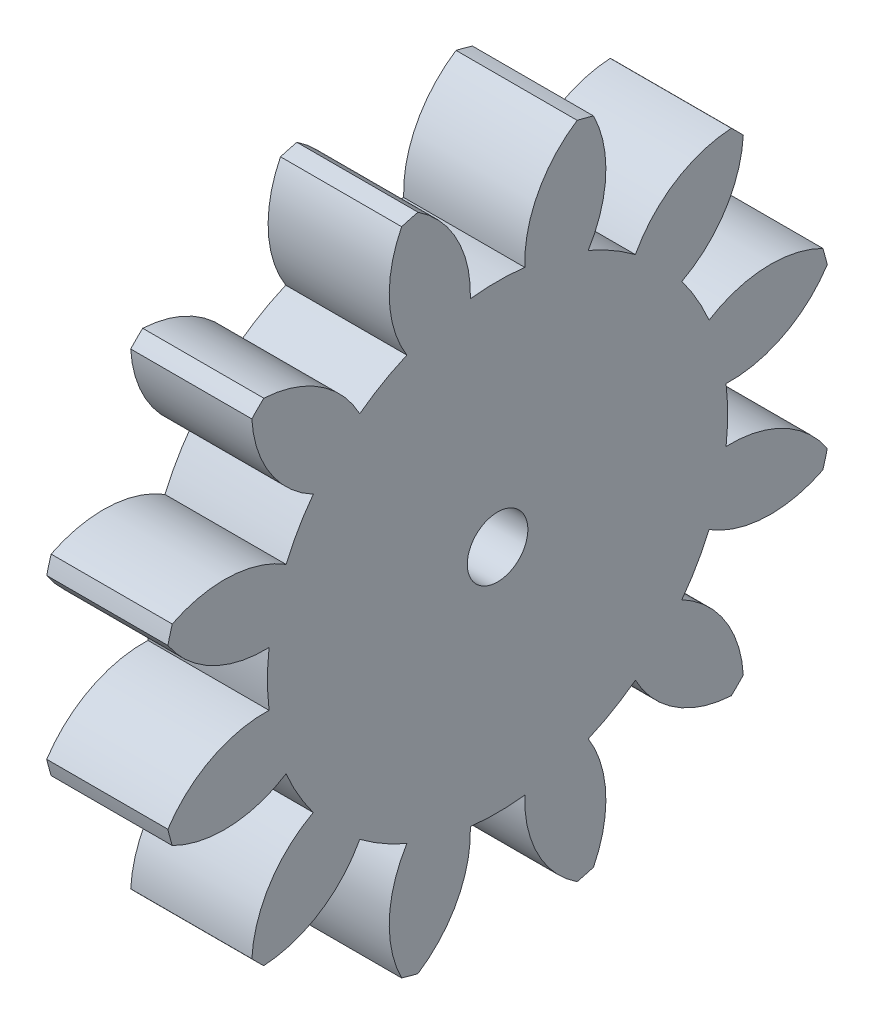
SolidWorks part; units mm, degrees
ref_plane "Plane1" through (0, 0, 0) normal (0, 0, 1) x (1, 0, 0)
ref_plane "Plane2" through (0, 0, 0) normal (0, 1, 0) x (1, 0, 0)
ref_plane "Plane3" through (0, 0, 0) normal (1, 0, 0) x (0, 0, -1)
other "Configuration Table"
sketch "HoldingSke" plane through (0, 0, 0) normal (0, 1, 0) x (1, 0, 0)
  line L0 (0, 0) -> (124.2247, -26.4048)
  line L1 (-15, 0) -> (100, 0) construction
  line L2 (0, 0) -> (-2.1039, 2.3779)
  line L3 (0, 0) -> (-11.863, 4.5341)
  line L4 (0, 0) -> (8.4473, 1.7955)
  line L5 (0, 0) -> (-47.5972, -17.7524)
  line L6 (0, 0) -> (-10.5278, -7.1032)
  line L7 (-2.1039, 2.3779) -> (8.8308, 51.9871)
  line L8 (-76.2, 54.61) -> (-69.596, 54.61)
  line L9 (-71.009, 38.7566) -> (-53.1078, 45.2721)
  line L10 (-76.2, 71.12) -> (104.1128, 71.12)
  line L11 (0, 0) -> (-12.7, 0)
  line L12 (-76.2, 101.6) -> (-76.0095, 101.6)
  line L13 (24.9733, 27.94) -> (52.9518, 28.4284)
  line L14 (24.9733, 27.94) -> (24.9746, 27.94)
  line L15 (24.9733, 27.94) -> (100.4006, 29.5858)
  circle A0 centre (0, 0) radius 3.175
  circle A1 centre (0, 0) radius 24.1287
  circle A2 centre (0, 0) radius 38.1
  circle A3 centre (0, 0) radius 3.175
  dimension "Hub_dia" = 76.2
  dimension "Bore" = 6.35
  dimension "MBD" = 6.35
  dimension "Pitch" = 127
  dimension "Overall_len" = 50.8
  dimension "Thickness" = 12.7
  dimension "OAL" = 50.8001
  dimension "T_dim" = 6.604
  dimension "Ap" = 20
  dimension "H" = 19.05
  dimension "Pitch_radius" = 180.3128
  dimension "Width" = 12.7
  dimension "Backlash" = 0.1905
  dimension "Addendum_fac" = 1
  dimension "Dedendum_fac" = 1.25
  dimension "Clearance_fac" = 0.25
  dimension "Dedendum_add" = 0.0013
sketch "BasProSke" plane through (0, 0, 0) normal (0, 1, 0) x (1, 0, 0)
  line L0 (-10, 0) -> (60, 0) construction
  line L1 (0, 0) -> (0, 35.56)
  line L2 (0, 0) -> (12.7, 0)
  line L3 (12.7, 0) -> (12.7, 35.56)
  line L4 (12.7, 35.56) -> (0, 35.56)
  dimension "Thickness" = 12.7
revolve "Base-Revolve" add sketch "BasProSke" angle 360 about L0
sketch "TooCutSke" plane through (0, 0, 0) normal (1, 0, 0) x (0, 0, -1)
  line L1 (0, 0) -> (0, 107) construction
  line L2 (0, 0) -> (-4.3113, 30.1735) construction
  line L3 (0, 0) -> (-15.6644, 58.4603) construction
  line L4 (-4.3113, 30.1735) -> (-7.8322, 29.2301) construction
  arc A0 (2.8524, 23.9595) -> (-2.8524, 23.9595) centre (0, 0) ccw
  arc A1 (8.3729, 34.5864) -> (-8.3729, 34.5864) centre (0, 0) ccw
  circle A2 centre (0, 0) radius 30.48 construction
  circle A3 centre (0, 0) radius 28.6418 construction
  arc A4 (-2.8524, 23.9595) -> (-8.3729, 34.5864) centre (-15.0372, 24.377) ccw
  arc A5 (8.3729, 34.5864) -> (2.8524, 23.9595) centre (15.0372, 24.377) ccw
  dimension "Pitch_dia" = 60.96
extrude "ToothCut" cut sketch "TooCutSke" along normal through all
fillet "Breaks" [suppressed] radius 0.1016
fillet "RootFillets" [suppressed] radius 1.2713
pattern_circular "TeethCuts" count 12 every 30 about axis through (-10, 0, 0) along (1, 0, 0) of "ToothCut", "RootFillets", "Breaks"
sketch "HubNeaOneSke" plane through (0, 0, 0) normal (-1, 0, 0) x (0, 0, 1)
  circle A0 centre (0, 0) radius 24.1287
extrude "HubNearOne" [suppressed] add sketch "HubNeaOneSke" along normal blind 38.1001
sketch "HubNeaBotSke" plane through (0, 0, 0) normal (-1, 0, 0) x (0, 0, 1)
  circle A0 centre (0, 0) radius 24.1287
extrude "HubNearBoth" [suppressed] add sketch "HubNeaBotSke" along normal blind 19.05
ref_plane "FarPln" through (12.7, 0, 0) normal (1, 0, 0) x (0, 0, -1)
sketch "HubFarSke" plane through (12.7, 0, 0) normal (1, 0, 0) x (0, 0, -1)
  circle A0 centre (0, 0) radius 24.1287
extrude "HubFar" [suppressed] add sketch "HubFarSke" along normal blind 19.05
sketch "BorSke" plane through (0, 0, 0) normal (1, 0, 0) x (0, 0, -1)
  circle A0 centre (0, 0) radius 3.175
  dimension "Diameter" = 6.35
extrude "Bore" cut sketch "BorSke" along normal mid plane 101.6001
sketch "KeySke" plane through (0, 0, 0) normal (1, 0, 0) x (0, 0, -1)
  line L0 (-0.127, 0) -> (-0.127, 3.429)
  line L1 (-0.127, 3.429) -> (0.127, 3.429)
  line L2 (0.127, 3.429) -> (0.127, 0)
  line L3 (0, 0) -> (0, 34) construction
  line L4 (-0.127, 0) -> (0.127, 0)
  dimension "Offset" = 3.429
  dimension "Width" = 0.254
extrude "Keyway" [suppressed] cut sketch "KeySke" along normal mid plane 101.6001
pattern_circular "Keyway2" [suppressed] count 2 every 90 about axis through (-10, 0, 0) along (1, 0, 0)
equation "' \"Pitch@HoldingSke\" = 4"
equation "' \"Num_teeth@HoldingSke\" = 12"
equation "' \"Ap@HoldingSke\" =  20"
equation "' \"Ap@HoldingSke\" = 20"
equation "' \"Width@HoldingSke\" = 0.5"
equation "' \"Hub_dia@HoldingSke\"= 1"
equation "' \"Hub_dia@HoldingSke\" = 1"
equation "' \"Overall_len@HoldingSke\" = 1.0"
equation "' \"Bore@HoldingSke\" = 0.75"
equation "' \"T_dim@HoldingSke\" = 0.85"
equation "' \"Width@KeySke\" = 0.25"
equation "' \"Show_teeth@HoldingSke\" = 13"
equation "' \"Backlash@HoldingSke\" = 0.009"
equation "' \"Addendum_fac@HoldingSke\" = 1.0"
equation "' \"Dedendum_fac@HoldingSke\" = 1.25"
equation "' \"Dedendum_add@HoldingSke\" = 0.00005"
equation "' \"Clearance_fac@HoldingSke\" = 0.25"
equation "' \"Pitch@HoldingSke\" = 0.5"
equation "' \"Num_teeth@HoldingSke\" = 23"
equation "' \"Show_teeth@HoldingSke\" = 23"
equation "' \"Backlash@HoldingSke\" = 0.0375"
equation "\"Overcut_dia@TooCutSke\" = (\"Num_teeth@HoldingSke\" + 2 * \"Addendum_fac@HoldingSke\") / \"Pitch@HoldingSke\" + 0.002"
equation "\"Pitch_dia@TooCutSke\" = \"Num_teeth@HoldingSke\" / \"Pitch@HoldingSke\""
equation "\"Base_dia@TooCutSke\" = \"Num_teeth@HoldingSke\" / \"Pitch@HoldingSke\" * cos((\"Ap@HoldingSke\"  * 3.14159265 / 180))"
equation "\"Root_dia@TooCutSke\" = (\"Num_teeth@HoldingSke\" + 2) / \"Pitch@HoldingSke\" - 2 * (\"Addendum_fac@HoldingSke\" + \"Dedendum_fac@HoldingSke\") / \"Pitch@HoldingSke\" - \"Dedendum_add@HoldingSke\" * 2"
equation "\"Half_ang@TooCutSke\" = 180 / \"Num_teeth@HoldingSke\""
equation "\"Half_CT@TooCutSke\" = \"Num_teeth@HoldingSke\" / \"Pitch@HoldingSke\" * sin((3.14159265 / 2 / \"Num_teeth@HoldingSke\")) / 2 - 7 * \"Backlash@HoldingSke\" / 4"
equation "\"Flank_rad@TooCutSke\" = \"Num_teeth@HoldingSke\" / \"Pitch@HoldingSke\" / 5"
equation "\"Radius@RootFillets\" = \"Clearance_fac@HoldingSke\" / \"Pitch@HoldingSke\" + \"Dedendum_add@HoldingSke\""
equation "\"Break_rad@Breaks\" = 0.02 / \"Pitch@HoldingSke\""
equation "\"Thickness@HoldingSke\" = \"Width@HoldingSke\""
equation "\"OAL@HoldingSke\" = \"Thickness@HoldingSke\""
equation "\"MHD@HoldingSke\" = (\"Num_teeth@HoldingSke\" + 2) / \"Pitch@HoldingSke\" - 2 * (\"Addendum_fac@HoldingSke\" + \"Dedendum_fac@HoldingSke\")  / \"Pitch@HoldingSke\" - \"Dedendum_add@HoldingSke\" * 2"
equation "\"MBD@HoldingSke\" = (\"Num_teeth@HoldingSke\" + 2) / \"Pitch@HoldingSke\" - 2 * (\"Addendum_fac@HoldingSke\" + \"Dedendum_fac@HoldingSke\")  / \"Pitch@HoldingSke\" - \"Dedendum_add@HoldingSke\" * 2 - 0.002"
equation "\"MHD@HoldingSke\" = ((sgn( \"MHD@HoldingSke\" - \"Hub_dia@HoldingSke\" )-1)*( \"MHD@HoldingSke\" - \"Hub_dia@HoldingSke\" ))/-2+ \"Hub_dia@HoldingSke\""
equation "\"MBD@HoldingSke\" = ((sgn( \"MBD@HoldingSke\" - \"Bore@HoldingSke\" )-1)*( \"MBD@HoldingSke\" - \"Bore@HoldingSke\" ))/-2+ \"Bore@HoldingSke\""
equation "\"OAL@HoldingSke\" = ((sgn( \"OAL@HoldingSke\" - \"Overall_len@HoldingSke\" )+1)*( \"OAL@HoldingSke\" - \"Overall_len@HoldingSke\" ))/2 + \"Overall_len@HoldingSke\" + 0.000002"
equation "\"Num_teeth@TeethCuts\" = int( \"Show_teeth@HoldingSke\" ) + 1"
equation "\"Num_teeth@TeethCuts\" = ((sgn( \"Num_teeth@TeethCuts\" - \"Num_teeth@HoldingSke\" )-1)*( \"Num_teeth@TeethCuts\" - \"Num_teeth@HoldingSke\" ))/-2+ \"Num_teeth@HoldingSke\""
equation "\"Num_teeth@TeethCuts\" = ((sgn( \"Num_teeth@TeethCuts\" - 2.0)+1)*( \"Num_teeth@TeethCuts\" - 2.0))/2 +2.0"
equation "\"Angle@TeethCuts\" = 360.0 / \"Num_teeth@HoldingSke\""
equation "\"Diameter@BasProSke\" = (\"Num_teeth@HoldingSke\" + 2 * \"Addendum_fac@HoldingSke\") / \"Pitch@HoldingSke\""
equation "\"Thickness@BasProSke\"  = \"Thickness@HoldingSke\""
equation "' \"Fillet_rad@BasProSke\" =  \"Thickness@HoldingSke\" * 0.05"
equation "' \"Fillet_rad@BasProSke\" = \"Thickness@HoldingSke\" * 0.05"
equation "\"MHD@HoldingSke\" = ((sgn( \"MHD@HoldingSke\" - \"Root_dia@TooCutSke\" )-1)*( \"MHD@HoldingSke\" - \"Root_dia@TooCutSke\" ))/-2+ \"Root_dia@TooCutSke\""
equation "\"Diameter@HubNeaOneSke\" = \"MHD@HoldingSke\""
equation "\"Length@HubNearOne\" = \"OAL@HoldingSke\" - \"Thickness@BasProSke\""
equation "\"Diameter@HubNeaBotSke\" = \"MHD@HoldingSke\""
equation "\"Length@HubNearBoth\" = ( \"OAL@HoldingSke\" - \"Thickness@BasProSke\" ) / 2.0"
equation "\"Thickness@FarPln\" = \"Thickness@BasProSke\""
equation "\"Diameter@HubFarSke\" = \"MHD@HoldingSke\""
equation "\"Length@HubFar\" = ( \"OAL@HoldingSke\" - \"Thickness@BasProSke\" ) / 2.0"
equation "\"Diameter@BorSke\" = \"MBD@HoldingSke\""
equation "\"D1@Bore\" = \"OAL@HoldingSke\" * 2.0"
equation "\"D1@Keyway\" = \"OAL@HoldingSke\" * 2.0"
equation "\"Offset@KeySke\" = \"T_dim@HoldingSke\" - \"MBD@HoldingSke\" / 2.0"
